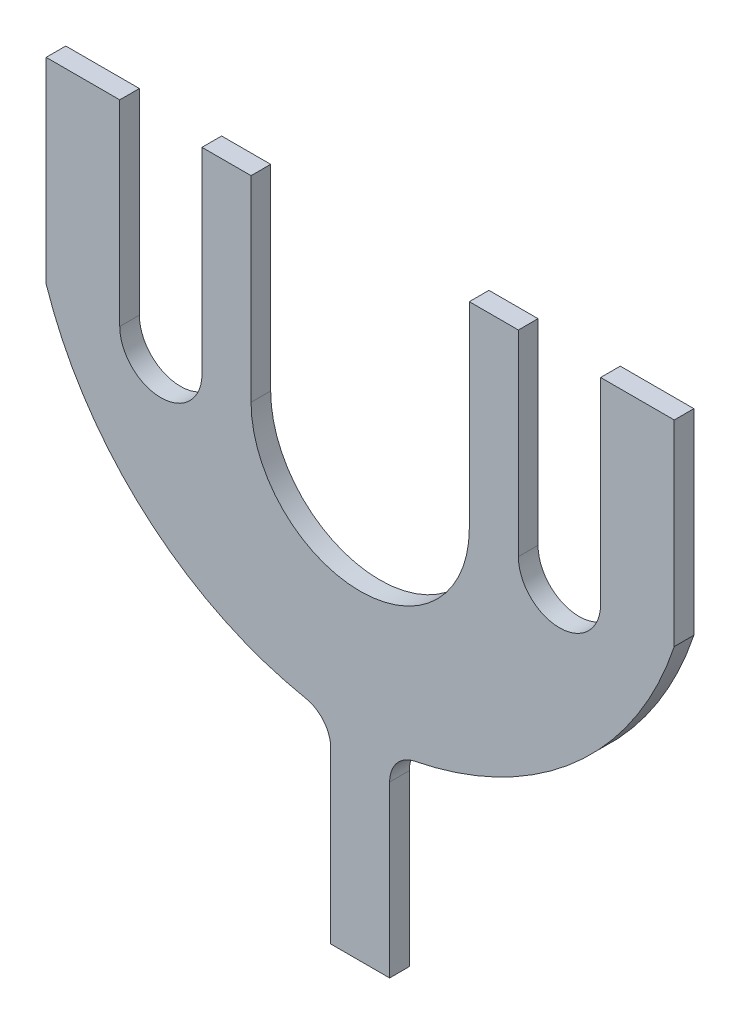
SolidWorks part; units mm, degrees
material "6061-T4 (SS)"
ref_plane "Front Plane" through (0, 0, 0) normal (0, 0, 1) x (1, 0, 0)
ref_plane "Top Plane" through (0, 0, 0) normal (0, 1, 0) x (1, 0, 0)
ref_plane "Right Plane" through (0, 0, 0) normal (1, 0, 0) x (0, 0, -1)
sketch "Sketch2" plane through (0, 0, 0) normal (0, 0, 1) x (1, 0, 0)
  line L0 (-21, 21.4878) -> (-17.25, 21.4878)
  line L1 (-21, 21.4878) -> (-21, 11.4878)
  line L2 (-10.56, 21.4878) -> (-10.56, 11.4878)
  line L3 (3.06, 21.4878) -> (3.06, 11.4878)
  line L4 (-21, 11.4878) -> (11, 11.4878) construction
  line L5 (11, 21.4878) -> (11, 8.9983) construction
  line L6 (-5, 11.4878) -> (-5, -10.3842) construction
  line L9 (-17.25, 11.4878) -> (-17.25, 21.4878)
  line L10 (11, 21.4878) -> (-25, 21.4878) construction
  line L13 (-13.06, 11.4878) -> (-13.06, 21.4878)
  line L14 (-13.06, 21.4878) -> (-10.56, 21.4878)
  line L16 (7.25, 11.4878) -> (7.25, 21.4878)
  line L17 (11, 11.4878) -> (11, 21.4878)
  line L23 (3.06, 21.4878) -> (0.56, 21.4878)
  line L24 (0.56, 21.4878) -> (0.56, 11.4878)
  line L25 (7.25, 21.4878) -> (11, 21.4878)
  line L28 (-6.5, -1.7375) -> (-6.5, -10.3842)
  line L29 (-6.5, -10.3842) -> (-3.5, -10.3842)
  line L30 (-3.5, -10.3842) -> (-3.5, -1.7375)
  arc A0 (-21, 11.4878) -> (-7.7797, -0.1802) centre (-4.3868, 16.9878) ccw
  arc A2 (-17.25, 11.4878) -> (-13.06, 11.4878) centre (-15.155, 11.4878) ccw
  arc A3 (3.06, 11.4878) -> (7.25, 11.4878) centre (5.155, 11.4878) ccw
  arc A4 (-10.56, 11.4878) -> (0.56, 11.4878) centre (-5, 11.4878) ccw
  arc A5 (11, 11.4878) -> (-2.2203, -0.1802) centre (-5.6132, 16.9878) cw
  arc A6 (-2.2203, -0.1802) -> (-3.5, -1.7375) centre (-1.9125, -1.7375) ccw
  arc A7 (-7.7797, -0.1802) -> (-6.5, -1.7375) centre (-8.0875, -1.7375) cw
  point P6 (-3.5, -0.3842)
  point P13 (-6.5, -0.3842)
  dimension "D1" = 2.5
  dimension "D9" = 17.5
  dimension "D10" = 17.5
  dimension "D11" = 32
  dimension "D13" = 1.5875
  dimension "D2" = 2.5
  dimension "D3" = 10
  dimension "D4" = 4.19
  dimension "D5" = 5.5
  dimension "D6" = 3
  dimension "D7" = 3.75
  dimension "D8" = 3.75
  dimension "D12" = 10
extrude "Boss-Extrude2" add sketch "Sketch2" along normal blind 1
